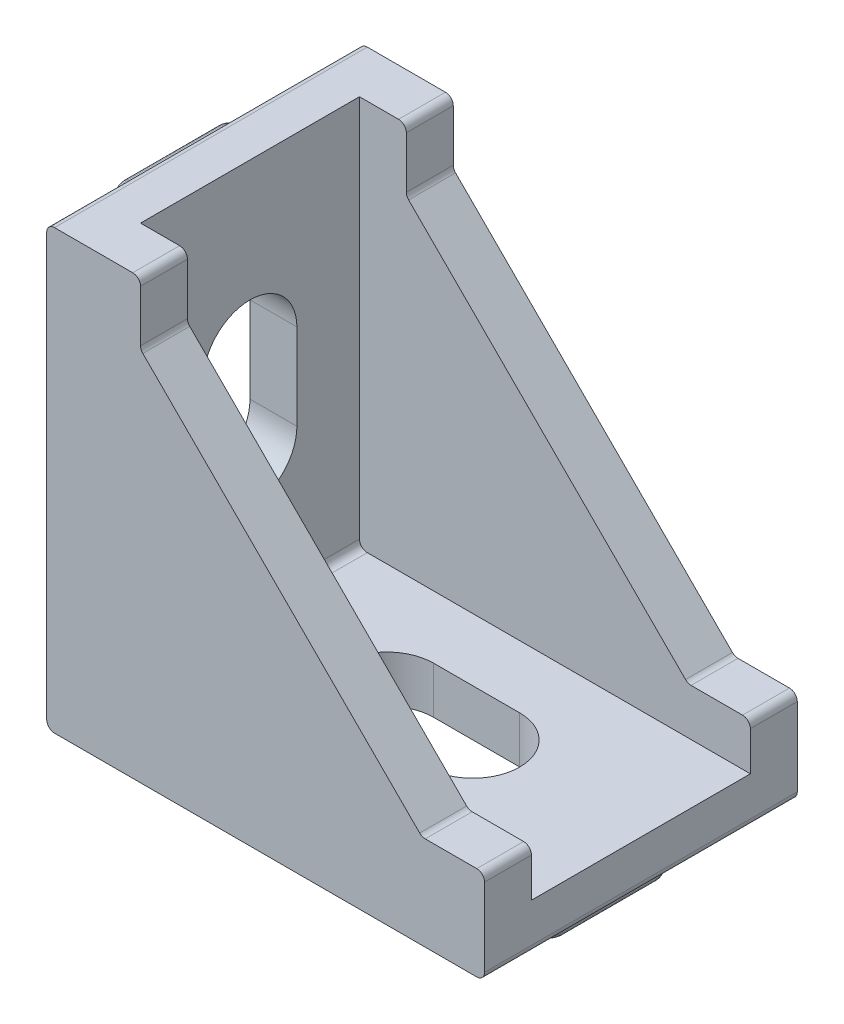
SolidWorks part; units mm, degrees
ref_plane "Front Plane" through (0, 0, 0) normal (0, 0, 1) x (1, 0, 0)
ref_plane "Top Plane" through (0, 0, 0) normal (0, 1, 0) x (1, 0, 0)
ref_plane "Right Plane" through (0, 0, 0) normal (1, 0, 0) x (0, 0, -1)
sketch "Sketch1" plane through (0, 0, 0) normal (0, 0, 1) x (1, 0, 0)
  line L0 (-8, 14) -> (-8, 10)
  line L1 (-14, 14) -> (14, 14)
  line L2 (-14, 14) -> (-14, -14)
  line L3 (-14, -14) -> (14, -14)
  line L4 (14, 14) -> (14, -14)
  line L5 (-14, 14) -> (14, -14) construction
  line L6 (-14, -14) -> (14, 14) construction
  line L7 (-8, 10) -> (10, -8)
  line L8 (10, -8) -> (14, -8)
  point P0 (0, 0)
  dimension "D1" = 28
  dimension "D2" = 28
  dimension "D3" = 6
  dimension "D4" = 6
  dimension "D5" = 4
  dimension "D6" = 4
extrude "Boss-Extrude1" add sketch "Sketch1" along normal blind 20 contours L8 L7 L0 L1 L2 L3 L4
sketch "Sketch2" plane through (0, 14, 0) normal (0, 1, 0) x (1, 0, 0)
  line L0 (-14, 0) -> (-8, 0) construction
  line L1 (-11, -3) -> (14, -3)
  line L2 (-11, -3) -> (-11, -17)
  line L3 (-11, -17) -> (14, -17)
  line L4 (14, -3) -> (14, -17)
  line L5 (-14, -20) -> (-14, 0) construction
  line L6 (-14, -20) -> (-8, -20) construction
  line L7 (14, -20) -> (14, 0) construction
  dimension "D1" = 3
  dimension "D2" = 3
  dimension "D3" = 3
extrude "Cut-Extrude1" cut sketch "Sketch2" against normal offset from surface (25 mm away) 3 up to face at (0, -14, 10)
sketch "Sketch3" plane through (0, -14, 0) normal (0, -1, 0) x (1, 0, 0)
  line L0 (-2.25, 10) -> (3.25, 10) construction
  line L1 (-2.25, 13) -> (3.25, 13)
  line L2 (-2.25, 7) -> (3.25, 7)
  line L3 (-14, 20) -> (-14, 0) construction
  arc A0 (-2.25, 13) -> (-2.25, 7) centre (-2.25, 10) ccw
  arc A1 (3.25, 7) -> (3.25, 13) centre (3.25, 10) ccw
  point P2 (0.5, 10)
  point P10 (-14, 10)
  dimension "D3" = 6
  dimension "D1" = 11.75
  dimension "D2" = 5.5
extrude "Cut-Extrude2" cut sketch "Sketch3" against normal through all
ref_plane "Plane1" through (0, 0, 0) normal (-0.7071, 0.7071, 0) x (0, 0, 1)
mirror "Mirror1" about plane through (0, 0, 0) normal (-0.7071, 0.7071, 0) of "Cut-Extrude2"
sketch "Sketch4" plane through (-14, 0, 0) normal (-1, 0, 0) x (0, 0, 1)
  line L0 (7, 11) -> (13, 11) construction
  line L1 (7, 12) -> (13, 12)
  line L2 (7, 10) -> (13, 10)
  line L3 (20, 14) -> (0, 14) construction
  line L4 (10, 0) -> (20, 0) construction
  line L5 (20, 14) -> (20, -14) construction
  line L6 (7, -11) -> (13, -11) construction
  line L7 (7, -12) -> (13, -12)
  line L8 (7, -10) -> (13, -10)
  arc A0 (7, 12) -> (7, 10) centre (7, 11) ccw
  arc A1 (13, 10) -> (13, 12) centre (13, 11) ccw
  arc A2 (7, -12) -> (7, -10) centre (7, -11) cw
  arc A3 (13, -10) -> (13, -12) centre (13, -11) cw
  point P2 (10, 11)
  point P10 (10, 14)
  point P16 (10, -11)
  dimension "D2" = 1
  dimension "D1" = 6
  dimension "D3" = 20
extrude "Boss-Extrude2" add sketch "Sketch4" along normal blind 2
mirror "Mirror4" about plane through (0, 0, 0) normal (-0.7071, 0.7071, 0) of "Boss-Extrude2"
fillet "Fillet2" [suppressed] radius 1
fillet "Fillet3" [suppressed] radius 0.5
fillet "Fillet4" radius 0.5 12 edges at (-11, -11, 10) (-14, -14, 10) (14, -14, 10) (-14, 14, 10) (-8, 14, 1.5) (-8, 14, 18.5) (-8, 10, 1.5) (-8, 10, 18.5) (10, -8, 1.5) (10, -8, 18.5) (14, -8, 1.5) (14, -8, 18.5)
fillet "Fillet5" radius 0.2 16 edges at (-12, -16, 10) (-11, -16, 14) (-10, -16, 10) (-11, -16, 6) (10, -16, 10) (11, -16, 14) (12, -16, 10) (11, -16, 6) (-16, 12, 10) (-16, 11, 14) (-16, 10, 10) (-16, 11, 6) (-16, -10, 10) (-16, -11, 14) (-16, -12, 10) (-16, -11, 6)
